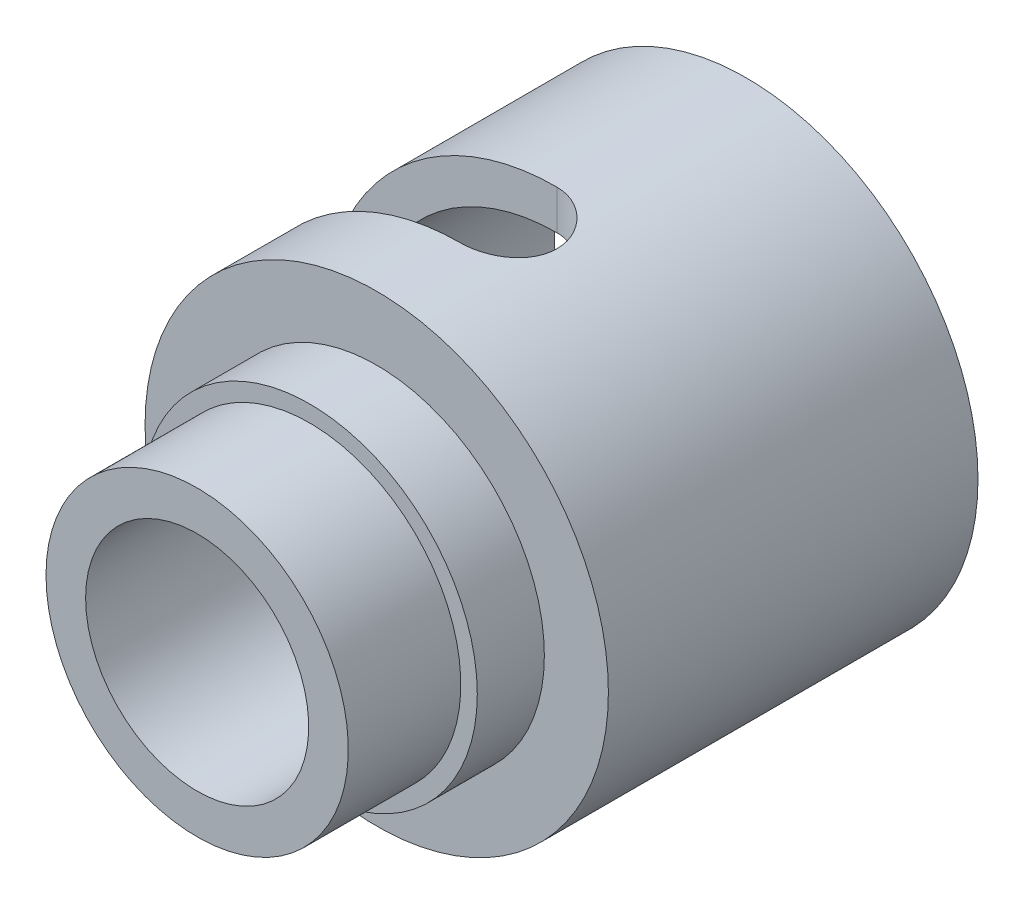
SolidWorks part; units mm, degrees
material "6061-T6 (SS)"
ref_plane "Front Plane" through (0, 0, 0) normal (0, 0, 1) x (1, 0, 0)
ref_plane "Top Plane" through (0, 0, 0) normal (0, 1, 0) x (1, 0, 0)
ref_plane "Right Plane" through (0, 0, 0) normal (1, 0, 0) x (0, 0, -1)
sketch "Sketch1" plane through (0, 0, 0) normal (1, 0, 0) x (0, 0, -1)
  line L0 (0, 0) -> (-42.3399, 0) construction
  line L1 (0, 0) -> (0, 49.8347) construction
  line L2 (0, 5.725) -> (0, 4.225)
  line L3 (0, 5.725) -> (4.262, 5.725)
  line L4 (4.262, 5.725) -> (4.262, 6.35)
  line L5 (4.262, 6.35) -> (6.802, 6.35)
  line L6 (6.802, 6.35) -> (6.802, 8.7754)
  line L7 (6.802, 8.7754) -> (20.802, 8.7754)
  line L8 (20.802, 8.7754) -> (20.802, 7.2754)
  line L9 (20.802, 7.2754) -> (7.802, 7.2754)
  line L10 (7.802, 7.2754) -> (7.802, 4.225)
  line L11 (7.802, 4.225) -> (0, 4.225)
  dimension "D1" = 11.45
  dimension "D2" = 8.45
  dimension "D3" = 4.262
  dimension "D4" = 12.7
  dimension "D5" = 2.54
  dimension "D6" = 1
  dimension "D7" = 14.5508
  dimension "D8" = 1.5
  dimension "D9" = 13
revolve "Revolve1" add sketch "Sketch1" angle 360 about L0
sketch "Sketch2" plane through (0, 0, 0) normal (0, 1, 0) x (1, 0, 0)
  line L0 (0, 0) -> (0, 2.9235) construction
  line L2 (-6.35, 6.802) -> (6.35, 6.802) construction
  circle A0 centre (0, 11.802) radius 1.8288
  dimension "D1" = 3.6576
  dimension "D2" = 5
extrude "Cut-Extrude1" cut sketch "Sketch2" along normal through all
sketch "Sketch3" plane through (0, 0, 0) normal (1, 0, 0) x (0, 0, -1)
  circle A0 centre (11.802, 0) radius 1.8288
  dimension "D1" = 3.6576
extrude "Cut-Extrude2" cut sketch "Sketch3" against normal through all
ref_plane "Plane1" through (0, 0, -13.6308) normal (0, 0, 1) x (1, 0, 0)
ref_plane "Plane2" through (0, 0, -9.9732) normal (0, 0, -1) x (-1, 0, 0)
sketch "Sketch4" plane through (0, 0, -9.9732) normal (0, 0, -1) x (-1, 0, 0)
  line L0 (0, 0) -> (0, 8.7754)
  line L1 (0, 0) -> (8.7754, 0)
  circle A0 centre (0, 0) radius 8.7754 construction
  arc A1 (8.7754, 0) -> (0, 8.7754) centre (0, 0) ccw
extrude "Cut-Extrude3" cut sketch "Sketch4" along normal up to surface (3.6576 mm away)
